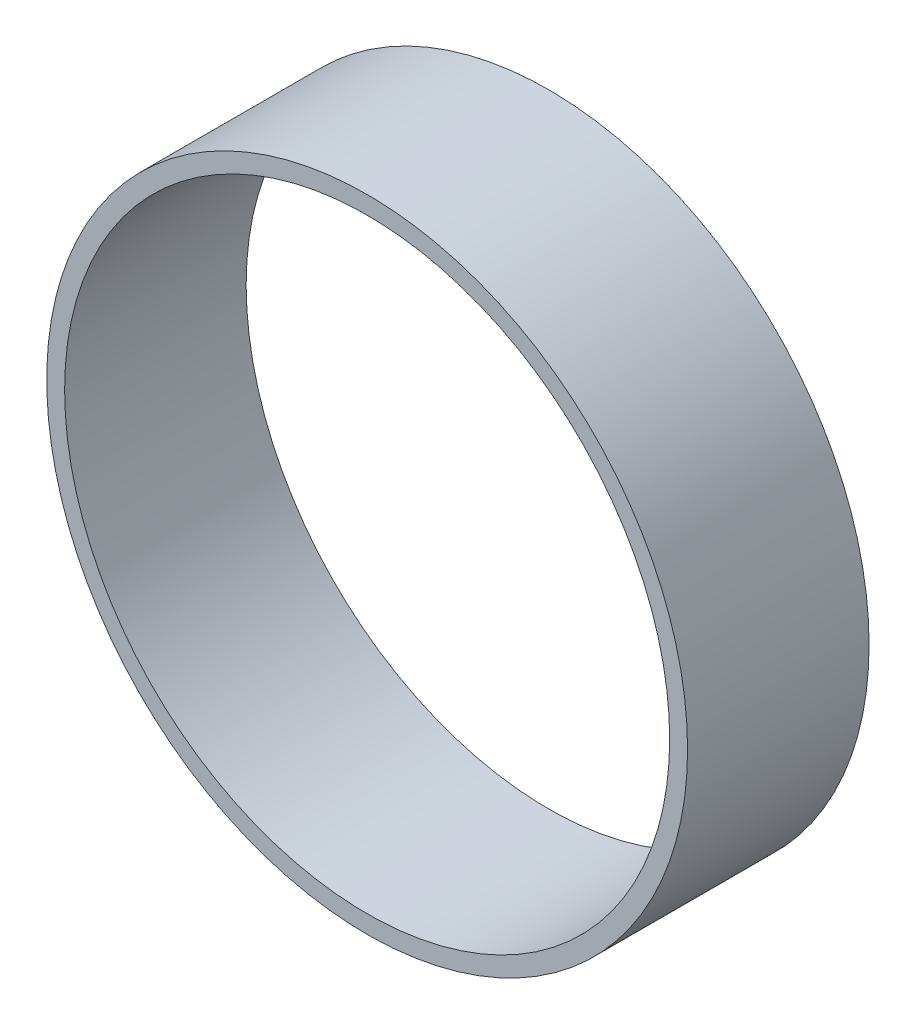
SolidWorks part; units mm, degrees
ref_plane "Front Plane" through (0, 0, 0) normal (0, 0, 1) x (1, 0, 0)
ref_plane "Top Plane" through (0, 0, 0) normal (0, 1, 0) x (1, 0, 0)
ref_plane "Right Plane" through (0, 0, 0) normal (1, 0, 0) x (0, 0, -1)
sketch "Sketch1" plane through (0, 0, 0) normal (0, 0, 1) x (1, 0, 0)
  circle A0 centre (0, 0) radius 38.1
  circle A1 centre (0, 0) radius 40.3541
  dimension "D1" = 76.2
extrude "Boss-Extrude1" add sketch "Sketch1" along normal blind 22.86
